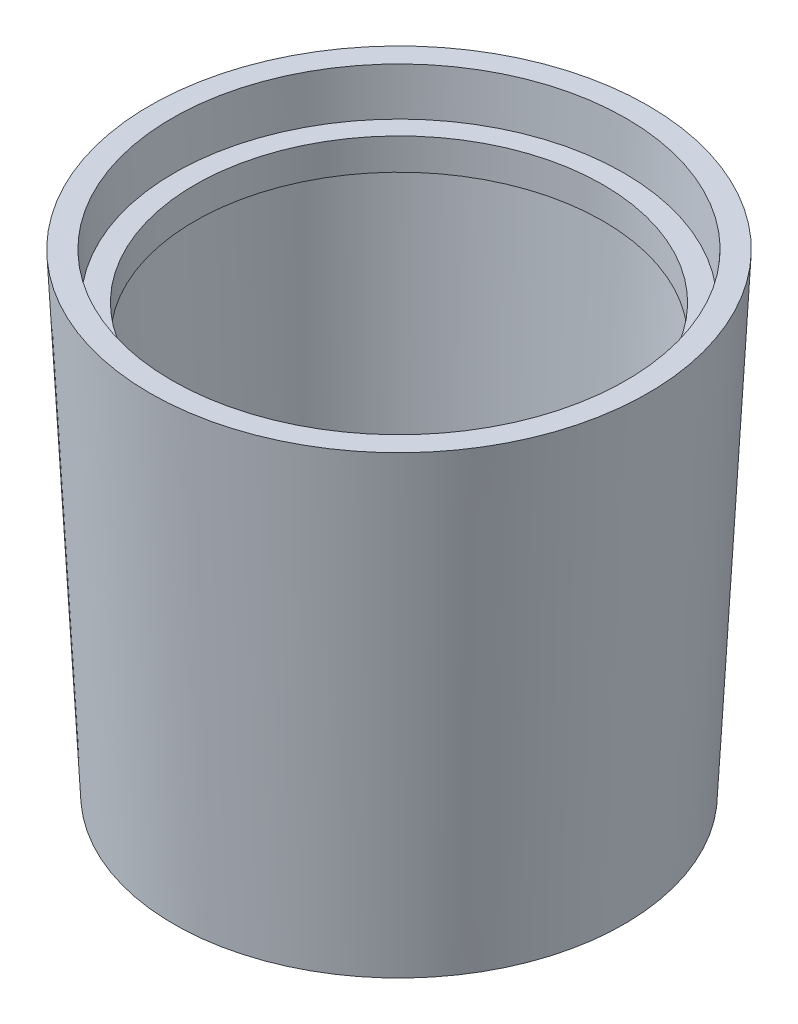
SolidWorks part; units mm, degrees
ref_plane "前视基准面" through (0, 0, 0) normal (0, 0, 1) x (1, 0, 0)
ref_plane "上视基准面" through (0, 0, 0) normal (0, 1, 0) x (1, 0, 0)
ref_plane "右视基准面" through (0, 0, 0) normal (1, 0, 0) x (0, 0, -1)
sketch "草图1" plane through (0, 0, 0) normal (0, 0, 1) x (1, 0, 0)
  line L0 (-383.4481, 0) -> (-295.032, 0)
  line L1 (-383.4481, 0) -> (-383.4481, 48.4972)
  line L2 (-295.032, 0) -> (-246.3348, 957.9563)
  line L3 (-246.3348, 957.9563) -> (-291.0605, 957.9563)
  line L4 (-291.0605, 957.9563) -> (-295.8157, 864.4132)
  line L5 (-295.8157, 864.4132) -> (-337.7226, 864.4132)
  line L6 (-337.7226, 864.4132) -> (-337.7226, 800.6881)
  line L7 (-299.8933, 800.6881) -> (-338.1305, 48.4972)
  line L8 (-337.7226, 800.6881) -> (-299.8933, 800.6881)
  line L9 (-383.4481, 48.4972) -> (-338.1305, 48.4972)
  line L10 (-383.4481, 0) -> (-752, 0) construction
  line L11 (-752, 0) -> (-752, 109.4948) construction
  point P2 (-366.0069, 954.1172)
  point P3 (-259.8775, 957.9563)
  point P14 (-647.7319, 9.597)
  point P15 (-308.5747, 0)
revolve "旋转1" add sketch "草图1" angle 360 about L11
